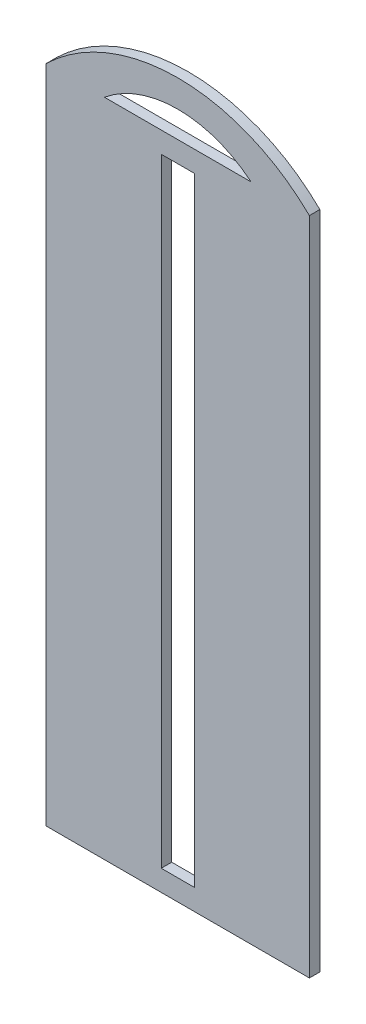
SolidWorks part; units mm, degrees
ref_plane "Front Plane" through (0, 0, 0) normal (0, 0, 1) x (1, 0, 0)
ref_plane "Top Plane" through (0, 0, 0) normal (0, 1, 0) x (1, 0, 0)
ref_plane "Right Plane" through (0, 0, 0) normal (1, 0, 0) x (0, 0, -1)
sketch "Sketch1" plane through (0, 0, 0) normal (0, 0, 1) x (1, 0, 0)
  line L0 (17.653, 200.025) -> (62.103, 200.025)
  line L1 (0, 0) -> (79.756, 0)
  line L2 (0, 0) -> (0, 200.025)
  line L4 (79.756, 0) -> (79.756, 200.025)
  line L5 (39.878, 0) -> (39.878, 200.025) construction
  line L6 (0, 200.025) -> (79.756, 200.025) construction
  line L7 (34.878, 6.35) -> (44.878, 6.35)
  line L8 (34.878, 6.35) -> (34.878, 193.675)
  line L9 (34.878, 193.675) -> (44.878, 193.675)
  line L10 (44.878, 6.35) -> (44.878, 193.675)
  line L11 (34.878, 6.35) -> (44.878, 193.675) construction
  line L12 (34.878, 193.675) -> (44.878, 6.35) construction
  arc A0 (0, 200.025) -> (79.756, 200.025) centre (39.878, 159.0876) cw
  arc A1 (17.653, 200.025) -> (62.103, 200.025) centre (39.878, 173.0842) cw
  point P9 (39.878, 200.025)
  point P10 (39.878, 0)
  point P15 (39.878, 100.0125)
  dimension "D4" = 34.925
  dimension "D5" = 57.15
  dimension "D1" = 200.025
  dimension "D2" = 79.756
  dimension "D3" = 44.45
  dimension "D6" = 10
  dimension "D7" = 6.35
extrude "Boss-Extrude1" add sketch "Sketch1" against normal blind 3.175
